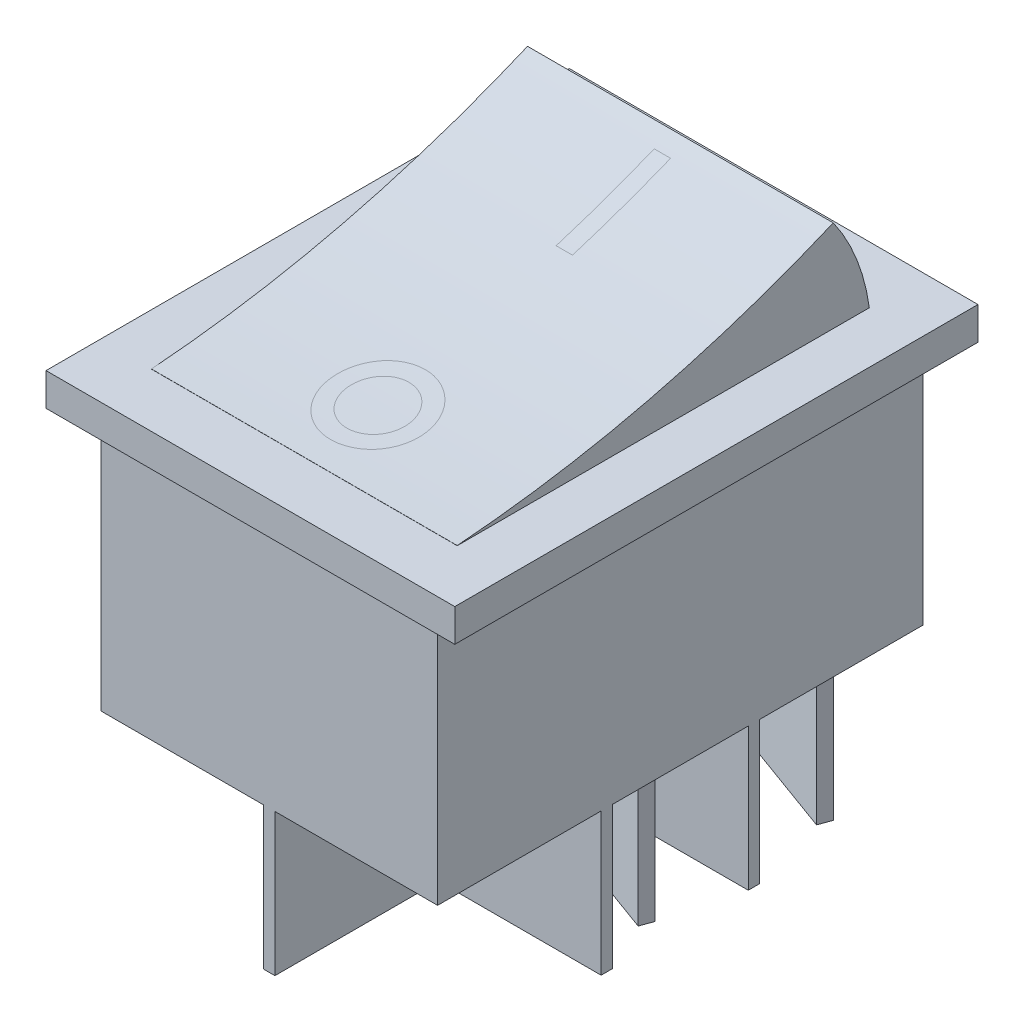
SolidWorks part; units mm, degrees
ref_plane "FRONT" through (0, 0, 0) normal (0, 0, 1) x (1, 0, 0)
ref_plane "TOP" through (0, 0, 0) normal (0, 1, 0) x (1, 0, 0)
ref_plane "RIGHT" through (0, 0, 0) normal (1, 0, 0) x (0, 0, -1)
sketch "Sketch1" plane through (0, 0, 0) normal (0, 0, 1) x (1, 0, 0)
  line L0 (12.5, 26.2) -> (-12.5, 26.2)
  line L1 (-12.5, 26.2) -> (-12.5, 24.2)
  line L2 (-12.5, 24.2) -> (-10.3, 24.2)
  line L3 (-10.3, 24.2) -> (-10.3, 0)
  line L4 (-10.3, 0) -> (10.3, 0)
  line L5 (0, 26.2) -> (0, 0) construction
  line L6 (10.3, 24.2) -> (10.3, 0)
  line L7 (12.5, 24.2) -> (10.3, 24.2)
  line L8 (12.5, 26.2) -> (12.5, 24.2)
  dimension "D1" = 25
  dimension "D2" = 20.6
  dimension "D3" = 2
  dimension "D4" = 26.2
extrude "Extrude1" add sketch "Sketch1" along normal mid plane 29.7
sketch "Sketch2" plane through (0, 0, 14.85) normal (0, 0, 1) x (1, 0, 0)
  line L1 (-12.5, 26.2) -> (12.5, 26.2)
  line L2 (-12.5, 26.2) -> (-12.5, 24.2)
  line L3 (-12.5, 24.2) -> (12.5, 24.2)
  line L4 (12.5, 26.2) -> (12.5, 24.2)
extrude "Extrude2" add sketch "Sketch2" along normal blind 1.15
mirror "Mirror1" about plane through (0, 0, 0) normal (0, 0, 1) of "Extrude2"
sketch "Sketch4" plane through (0, 0, 0) normal (1, 0, 0) x (0, 0, -1)
  line L0 (-12.7, 26.2) -> (-12.7, 26.21)
  line L1 (-16, 26.2) -> (16, 26.2) construction
  line L2 (-12.7, 26.2) -> (12.5, 26.2)
  line L3 (-16, 24.2) -> (-16, 26.2) construction
  line L5 (-16, 26.2) -> (16, 26.2) construction
  line L6 (16, 24.2) -> (16, 26.2) construction
  line L7 (0, 0) -> (0, 31.2367) construction
  arc A0 (-12.7, 26.21) -> (10.3, 31.8) centre (-18.2122, 99.0016) ccw
  arc A1 (10.3, 31.8) -> (12.5, 26.2) centre (0, 24.5214) cw
  dimension "D6" = 73
  dimension "D1" = 3.3
  dimension "D2" = 3.5
  dimension "D3" = 0.01
  dimension "D4" = 5.6
  dimension "D5" = 5.7
extrude "Extrude4" add sketch "Sketch4" along normal mid plane 18.7
sketch "Sketch5" plane through (0, 0, 0) normal (0, -1, 0) x (1, 0, 0)
  line L0 (0, 0) -> (0, 6.2202) construction
  line L1 (0, 0) -> (4.408, 0) construction
  line L2 (10.3, 14.85) -> (10.3, -14.85) construction
  line L3 (10.3, 14.85) -> (0.35, 14.85)
  line L4 (10.3, 14.85) -> (10.3, 4.85)
  line L5 (10.3, 4.85) -> (0.35, 4.85)
  line L6 (0.35, 14.85) -> (0.35, 4.85)
  line L7 (10.3, 4.15) -> (0.35, 4.15)
  line L8 (10.3, 4.15) -> (10.3, -4.15)
  line L9 (10.3, -4.15) -> (0.35, -4.15)
  line L10 (0.35, 4.15) -> (0.35, -4.15)
  line L11 (-0.35, 14.85) -> (-0.35, 4.85)
  line L12 (-10.3, 4.85) -> (-0.35, 4.85)
  line L13 (-10.3, 14.85) -> (-10.3, 4.85)
  line L14 (-10.3, 14.85) -> (-0.35, 14.85)
  line L15 (-10.3, -14.85) -> (-0.35, -14.85)
  line L16 (-10.3, -14.85) -> (-10.3, -4.85)
  line L17 (-10.3, -4.85) -> (-0.35, -4.85)
  line L18 (-0.35, -14.85) -> (-0.35, -4.85)
  line L19 (0.35, -14.85) -> (0.35, -4.85)
  line L20 (10.3, -4.85) -> (0.35, -4.85)
  line L21 (10.3, -14.85) -> (10.3, -4.85)
  line L22 (10.3, -14.85) -> (0.35, -14.85)
  line L23 (-0.35, 4.15) -> (-0.35, -4.15)
  line L24 (-10.3, -4.15) -> (-0.35, -4.15)
  line L25 (-10.3, 4.15) -> (-10.3, -4.15)
  line L26 (-10.3, 4.15) -> (-0.35, 4.15)
  dimension "D1" = 0.7
  dimension "D2" = 0.7
  dimension "D3" = 8.3
extrude "Cut-Extrude1" cut sketch "Sketch5" against normal blind 8.7
sketch "Sketch6" plane through (0, 0, 0) normal (0, 1, 0) x (1, 0, 0)
  line L0 (0, 0) -> (0, 18.021) construction
  line L1 (-0.5, 9.2) -> (0.5, 9.2)
  line L2 (-0.5, 9.2) -> (-0.5, 3.2)
  line L3 (-0.5, 3.2) -> (0.5, 3.2)
  line L4 (0.5, 9.2) -> (0.5, 3.2)
  line L5 (9.35, 10.3) -> (-9.35, 10.3) construction
  line L6 (9.35, -12.7) -> (-9.35, -12.7) construction
  circle A0 centre (0, -8.2) radius 1.9 construction
  circle A1 centre (0, -8.2) radius 2.9 construction
  dimension "D4" = 5.8
  dimension "D5" = 1
  dimension "D1" = 1
  dimension "D2" = 6
  dimension "D3" = 1.1
  dimension "D6" = 4.5
split line "Split Line3"
sketch "Sketch7" plane through (0, 0, 0) normal (0, 1, 0) x (1, 0, 0)
  line L0 (0, 0) -> (0, -14.0762) construction
  line L3 (-0.0005, -5.3) -> (-0.0005, -6.3)
  line L5 (0.0005, -5.3) -> (0.0005, -6.3)
  circle A0 centre (0, -8.2) radius 1.9 construction
  arc A1 (-0.0005, -6.3) -> (0.0005, -6.3) centre (0, -8.2) ccw
  circle A2 centre (0, -8.2) radius 2.9 construction
  arc A3 (-0.0005, -5.3) -> (0.0005, -5.3) centre (0, -8.2) ccw
  dimension "D1" = 0.001
split line "Split Line10"
sketch "Sketch9" plane through (0, 8.7, 0) normal (0, -1, 0) x (1, 0, 0)
  line L0 (-8.1456, -13.2057) -> (-2.2255, -11.0509)
  line L1 (-2.2255, -11.0509) -> (-2.4991, -10.2992)
  line L2 (-2.4991, -10.2992) -> (-8.4192, -12.4539)
  line L3 (-8.4192, -12.4539) -> (-8.1456, -13.2057)
  line L4 (-10.3, 14.85) -> (-10.3, -14.85) construction
  line L5 (2.6786, -13.2057) -> (8.5986, -11.0509)
  line L6 (8.5986, -11.0509) -> (8.325, -10.2992)
  line L7 (8.325, -10.2992) -> (2.405, -12.4539)
  line L8 (2.405, -12.4539) -> (2.6786, -13.2057)
  line L9 (-8.2417, -2.3925) -> (-2.3216, -0.2378)
  line L10 (-2.3216, -0.2378) -> (-2.5953, 0.5139)
  line L11 (-2.5953, 0.5139) -> (-8.5153, -1.6408)
  line L12 (-8.5153, -1.6408) -> (-8.2417, -2.3925)
  line L13 (2.5825, -2.3925) -> (8.5025, -0.2378)
  line L14 (8.5025, -0.2378) -> (8.2289, 0.5139)
  line L15 (8.2289, 0.5139) -> (2.3088, -1.6408)
  line L16 (2.3088, -1.6408) -> (2.5825, -2.3925)
  line L17 (-10.3, -4.85) -> (-10.3, -14.85) construction
  dimension "D1" = 0.8
  dimension "D2" = 6.3
  dimension "D3" = 70
  dimension "D4" = 1.7847
  dimension "D5" = 1.8808
  dimension "D6" = 12.6088
  dimension "D7" = 12.705
  dimension "D8" = 1.6443
  dimension "D9" = 12.4575
extrude "Extrude5" add sketch "Sketch9" along normal blind 9.3
